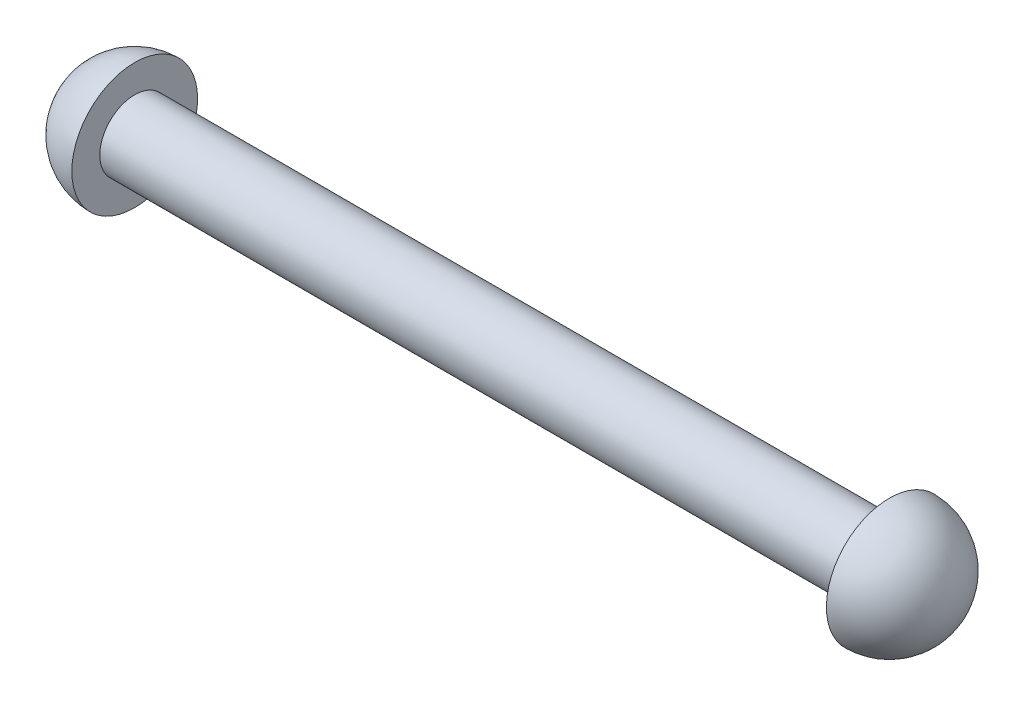
SolidWorks part; units mm, degrees
material "AISI 1020"
ref_plane "Front Plane" through (0, 0, 0) normal (0, 0, 1) x (1, 0, 0)
ref_plane "Top Plane" through (0, 0, 0) normal (0, 1, 0) x (1, 0, 0)
ref_plane "Right Plane" through (0, 0, 0) normal (1, 0, 0) x (0, 0, -1)
sketch "Sketch1" plane through (0, 0, 0) normal (0, 0, 1) x (1, 0, 0)
  line L0 (0, 0) -> (63.2872, 0) construction
  line L1 (5.715, 5.715) -> (5.715, 3.175)
  line L2 (5.715, 3.175) -> (74.295, 3.175)
  line L3 (0, 0) -> (0, 12.1658) construction
  line L4 (40.005, 3.175) -> (40.005, 0) construction
  line L5 (74.295, 5.715) -> (74.295, 3.175)
  line L6 (0, 0) -> (80.01, 0)
  arc A0 (0, 0) -> (5.715, 5.715) centre (5.715, 0) cw
  arc A1 (80.01, 0) -> (74.295, 5.715) centre (74.295, 0) ccw
  dimension "D2" = 5.715
  dimension "D1" = 34.29
  dimension "D3" = 6.35
  dimension "D4" = 11.43
revolve "Revolve1" add sketch "Sketch1" angle 360 about L6
